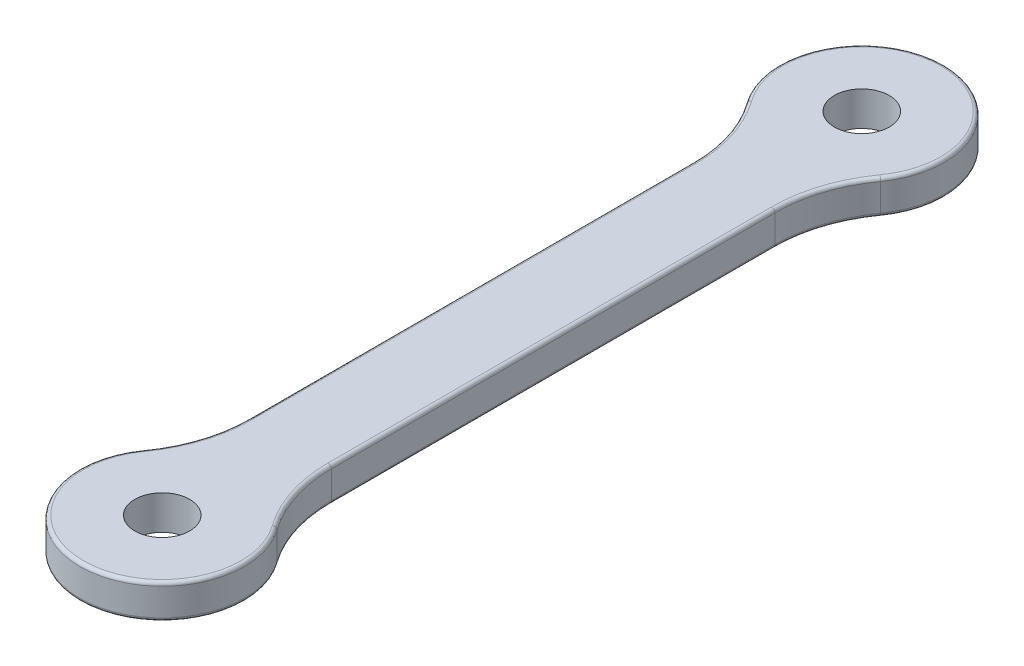
SolidWorks part; units mm, degrees
ref_plane "Front Plane" through (0, 0, 0) normal (0, 0, 1) x (1, 0, 0)
ref_plane "Top Plane" through (0, 0, 0) normal (0, 1, 0) x (1, 0, 0)
ref_plane "Right Plane" through (0, 0, 0) normal (1, 0, 0) x (0, 0, -1)
sketch "Sketch1" plane through (0, 0, 0) normal (0, 1, 0) x (1, 0, 0)
  line L1 (-3, -25.5) -> (3, -25.5)
  line L2 (-3, -25.5) -> (-3, 25.5)
  line L3 (-3, 25.5) -> (3, 25.5)
  line L4 (3, -25.5) -> (3, 25.5)
  line L5 (0, 25.5) -> (0, -25.5) construction
  line L6 (-3, 0) -> (3, 0) construction
  circle A0 centre (0, 25.5) radius 6
  circle A1 centre (0, 25.5) radius 2
  circle A2 centre (0, -25.5) radius 2
  circle A3 centre (0, -25.5) radius 6
  point P0 (0, 0)
  dimension "D2" = 12
  dimension "D5" = 4
  dimension "D3" = 51
  dimension "D4" = 6
extrude "Boss-Extrude1" add sketch "Sketch1" along normal blind 2.5 contours A3 L4 A0 L2 | A1 L4 A0 L2 | L2 A3 L4 A2 | L4 A3 L2 A2 | A1 L2 A0 L4
fillet "Fillet1" radius 10 4 edges at (-3, 1.25, 20.3038) (-3, 1.25, -20.3038) (3, 1.25, -20.3038) (3, 1.25, 20.3038)
fillet "Fillet2" radius 0.25 16 edges at (3.4803, 2.5, 19.2345) (3.4803, 0, 19.2345) (0, 2.5, 31.5) (0, 0, 31.5) (-3.4803, 2.5, 19.2345) (-3.4803, 0, 19.2345) (-3, 0, 0) (-3, 2.5, 0) (-3.4803, 2.5, -19.2345) (-3.4803, 0, -19.2345) (0, 0, -31.5) (0, 2.5, -31.5) (3.4803, 2.5, -19.2345) (3.4803, 0, -19.2345) (3, 0, 0) (3, 2.5, 0)
